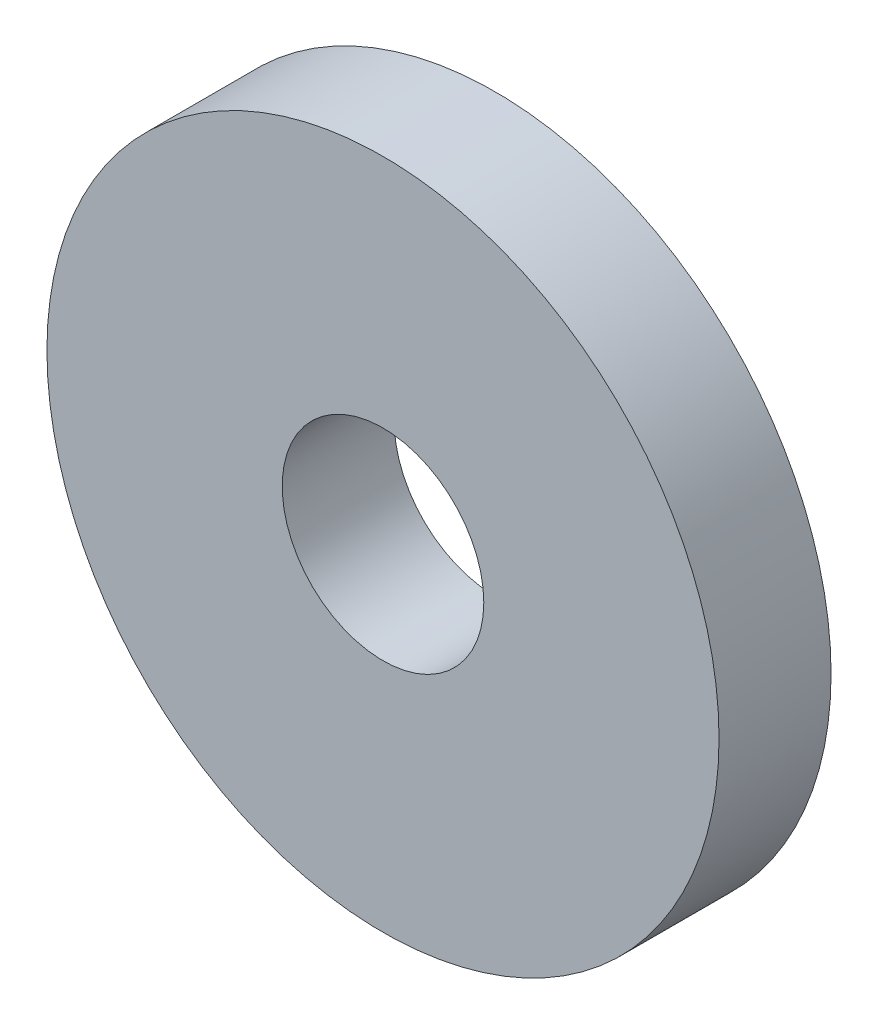
SolidWorks part; units mm, degrees
material "Maple"
ref_plane "Wasteboard" through (0, 0, 0) normal (0, 0, 1) x (1, 0, 0)
ref_plane "Left-Right" through (0, 0, 0) normal (0, 1, 0) x (1, 0, 0)
ref_plane "Front-Back" through (0, 0, 0) normal (1, 0, 0) x (0, 0, -1)
sketch "Sketch1" plane through (0, 0, 0) normal (0, 0, 1) x (1, 0, 0)
  circle A0 centre (0, 0) radius 30
  circle A1 centre (0, 0) radius 9
  dimension "D1" = 60
  dimension "D2" = 18
extrude "Boss-Extrude1" add sketch "Sketch1" along normal blind 10
